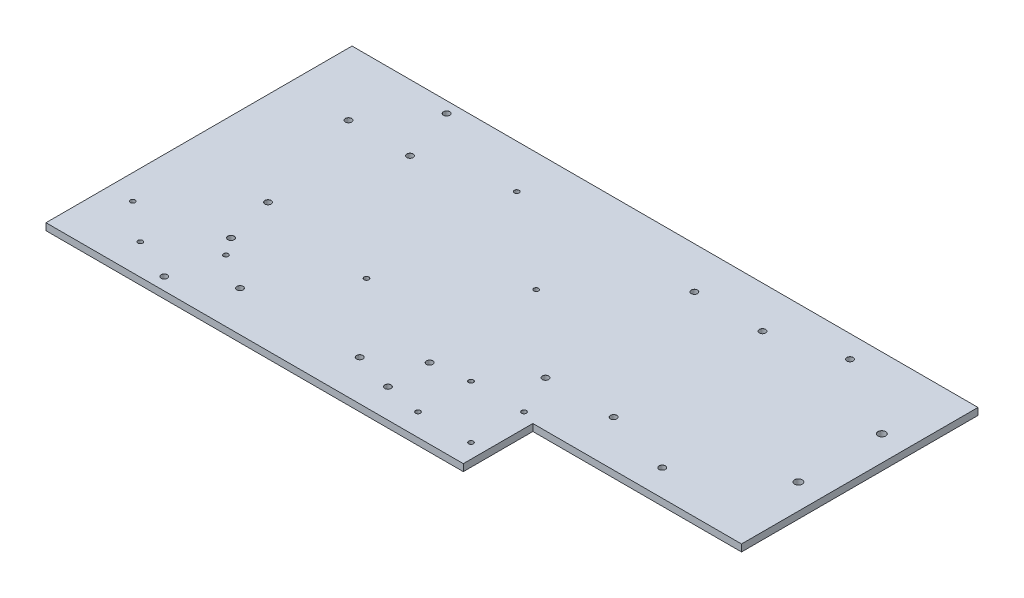
SolidWorks part; units mm, degrees
ref_plane "Front Plane" through (0, 0, 0) normal (0, 0, 1) x (1, 0, 0)
ref_plane "Top Plane" through (0, 0, 0) normal (0, 1, 0) x (1, 0, 0)
ref_plane "Right Plane" through (0, 0, 0) normal (1, 0, 0) x (0, 0, -1)
sketch "Sketch1" plane through (0, 0, 0) normal (0, 1, 0) x (1, 0, 0)
  line L0 (0, 0) -> (0, -220)
  line L1 (0, -220) -> (300, -220)
  line L2 (300, -220) -> (300, -170)
  line L3 (0, 0) -> (450, 0)
  line L4 (450, 0) -> (450, -170)
  line L5 (450, -170) -> (300, -170)
  dimension "D1" = 220
  dimension "D2" = 300
  dimension "D3" = 50
  dimension "D4" = 150
extrude "Boss-Extrude1" add sketch "Sketch1" along normal blind 5
sketch "Sketch2" plane through (0, 5, 0) normal (0, 1, 0) x (1, 0, 0)
  line L1 (450, 0) -> (0, 0) construction
  line L2 (0, -220) -> (300, -220) construction
  line L3 (0, 0) -> (0, -220) construction
  line L4 (300, -220) -> (300, -170) construction
  line L5 (300, -170) -> (450, -170) construction
  line L6 (289.58, -204.04) -> (251.48, -204.04) construction
  line L7 (289.58, -204.04) -> (289.58, -165.94) construction
  line L8 (289.58, -165.94) -> (251.48, -165.94) construction
  line L9 (251.48, -204.04) -> (251.48, -165.94) construction
  line L10 (276.07, -29.99) -> (325.07, -29.99) construction
  line L11 (276.07, -29.99) -> (276.07, -136.99) construction
  line L12 (276.07, -136.99) -> (325.07, -136.99) construction
  line L13 (325.07, -29.99) -> (325.07, -136.99) construction
  line L14 (450, -170) -> (450, 0) construction
  point P0 (17.79, -175.47)
  point P1 (84.79, -175.47)
  point P2 (45.79, -197.97)
  point P3 (44.95, -47.48)
  point P4 (89.15, -47.48)
  point P5 (67.05, -127.48)
  point P6 (225, -169.19)
  point P7 (225, -199.19)
  point P8 (251.48, -165.94)
  point P9 (289.58, -165.94)
  point P10 (289.58, -204.04)
  point P11 (251.48, -204.04)
  point P12 (149.84, -31.45)
  point P13 (149.84, -139.45)
  point P14 (217.84, -85.45)
  point P15 (276.07, -29.99)
  point P16 (325.07, -136.99)
  point P17 (431.86, -50.98)
  point P18 (431.86, -110.98)
  point P23 (325.07, -29.99)
  point P24 (110.5, -191)
  point P33 (196.5, -191)
  point P34 (276.07, -136.99)
  point P35 (0, 0)
  point P46 (176.8084, -191)
  dimension "D1" = 47.48
  dimension "D2" = 80
  dimension "D3" = 44.53
  dimension "D4" = 22.5
  dimension "D5" = 44.95
  dimension "D6" = 44.2
  dimension "D7" = 22.1
  dimension "D8" = 17.79
  dimension "D9" = 67
  dimension "D10" = 108
  dimension "D11" = 31.45
  dimension "D12" = 149.84
  dimension "D13" = 68
  dimension "D14" = 54
  dimension "D15" = 28
  dimension "D16" = 30
  dimension "D17" = 20.81
  dimension "D18" = 75
  dimension "D19" = 15.96
  dimension "D20" = 10.42
  dimension "D21" = 38.1
  dimension "D22" = 107
  dimension "D23" = 49
  dimension "D24" = 33.01
  dimension "D25" = 124.93
  dimension "D26" = 18.14
  dimension "D27" = 60
  dimension "D28" = 59.02
  dimension "D29" = 29
  dimension "D30" = 110.5
  dimension "D31" = 86
hole_wizard "M3 Clearance Hole1" positions "Sketch3" profile "Sketch4" hole size "M3" standard "ISO" end condition through all
sketch "Sketch3" plane through (0, 5, 0) normal (0, 1, 0) x (1, 0, 0)
  point P0 (17.79, -175.47)
  point P3 (45.79, -197.97)
  point P6 (84.79, -175.47)
  point P9 (251.48, -204.04)
  point P12 (251.48, -165.94)
  point P15 (149.84, -139.45)
  point P18 (217.84, -85.45)
  point P21 (149.84, -31.45)
  point P24 (289.58, -165.94)
  point P27 (289.58, -204.04)
sketch "Sketch4" plane through (17.79, 5, 175.47) normal (1, 0, 0) x (0, 0, 1)
  line L0 (0, 0) -> (0, 5)
  line L1 (0, 5) -> (1.7, 5)
  line L2 (1.7, 5) -> (1.7, 0.025)
  line L3 (1.7, 0.025) -> (1.725, 0)
  line L5 (1.725, 0) -> (0, 0)
  line L6 (-1.7, 0.025) -> (-1.725, 0) construction
  line L11 (0, -6.35) -> (0, 107.95) construction
  dimension "Thru Hole Dia." = 3.4
  dimension "Thru Hole Depth" = 5
  dimension "Near C'Sink Dia." = 3.45
  dimension "Near C'Sink Angle" = 90
hole_wizard "M4 Clearance Hole1" positions "Sketch7" profile "Sketch6" hole size "M4" standard "ISO" end condition through all
sketch "Sketch7" plane through (0, 5, 0) normal (0, 1, 0) x (1, 0, 0)
  point P0 (44.95, -47.48)
  point P3 (89.15, -47.48)
  point P6 (67.05, -127.48)
  point P9 (276.07, -29.99)
  point P12 (325.07, -29.99)
  point P15 (276.07, -136.99)
  point P18 (325.07, -136.99)
  point P21 (225, -199.19)
  point P24 (225, -169.19)
  point P27 (110.5, -191)
  point P30 (196.5, -191)
sketch "Sketch6" plane through (44.95, 5, 47.48) normal (1, 0, 0) x (0, 0, 1)
  line L0 (0, 0) -> (0, 5)
  line L1 (0, 5) -> (2.25, 5)
  line L2 (2.25, 5) -> (2.25, 0.025)
  line L3 (2.25, 0.025) -> (2.275, 0)
  line L5 (2.275, 0) -> (0, 0)
  line L6 (-2.25, 0.025) -> (-2.275, 0) construction
  line L11 (0, -6.35) -> (0, 107.95) construction
  dimension "Thru Hole Dia." = 4.5
  dimension "Thru Hole Depth" = 5
  dimension "Near C'Sink Dia." = 4.55
  dimension "Near C'Sink Angle" = 90
hole_wizard "M5 Clearance Hole1" positions "3DSketch1" profile "Sketch8" hole size "M5" standard "ISO" end condition through all
sketch3d "3DSketch1"
  point P0 (431.86, 5, 50.98)
  point P3 (431.86, 5, 110.98)
sketch "Sketch8" plane through (431.86, 5, 50.98) normal (1, 0, 0) x (0, 0, 1)
  line L0 (0, 0) -> (0, 5)
  line L1 (0, 5) -> (2.75, 5)
  line L2 (2.75, 5) -> (2.75, 0.025)
  line L3 (2.75, 0.025) -> (2.775, 0)
  line L5 (2.775, 0) -> (0, 0)
  line L6 (-2.75, 0.025) -> (-2.775, 0) construction
  line L11 (0, -6.35) -> (0, 107.95) construction
  dimension "Thru Hole Dia." = 5.5
  dimension "Thru Hole Depth" = 5
  dimension "Near C'Sink Dia." = 5.55
  dimension "Near C'Sink Angle" = 90
sketch "Sketch9" plane through (0, 5, 0) normal (0, 1, 0) x (1, 0, 0)
  line L0 (0, 0) -> (0, -220) construction
  line L1 (450, -170) -> (450, 0) construction
  line L2 (450, 0) -> (0, 0) construction
  line L3 (300, -170) -> (450, -170) construction
  line L4 (0, -220) -> (300, -220) construction
  point P0 (76, -8)
  point P1 (76, -163)
  point P2 (76, -211)
  point P3 (374, -151)
  point P4 (374, -16)
  dimension "D1" = 76
  dimension "D2" = 76
  dimension "D3" = 16
  dimension "D4" = 19
  dimension "D5" = 9
  dimension "D6" = 8
  dimension "D7" = 57
hole_wizard "M4 Clearance Hole2" positions "Sketch10" profile "Sketch11" hole size "M4" standard "ISO" end condition through all
sketch "Sketch10" plane through (0, 5, 0) normal (0, 1, 0) x (1, 0, 0)
  point P0 (76, -8)
  point P3 (76, -163)
  point P6 (76, -211)
  point P9 (374, -151)
  point P12 (374, -16)
sketch "Sketch11" plane through (76, 5, 8) normal (1, 0, 0) x (0, 0, 1)
  line L0 (0, 0) -> (0, 5)
  line L1 (0, 5) -> (2.25, 5)
  line L2 (2.25, 5) -> (2.25, 0.025)
  line L3 (2.25, 0.025) -> (2.275, 0)
  line L5 (2.275, 0) -> (0, 0)
  line L6 (-2.25, 0.025) -> (-2.275, 0) construction
  line L11 (0, -6.35) -> (0, 107.95) construction
  dimension "Thru Hole Dia." = 4.5
  dimension "Thru Hole Depth" = 5
  dimension "Near C'Sink Dia." = 4.55
  dimension "Near C'Sink Angle" = 90
